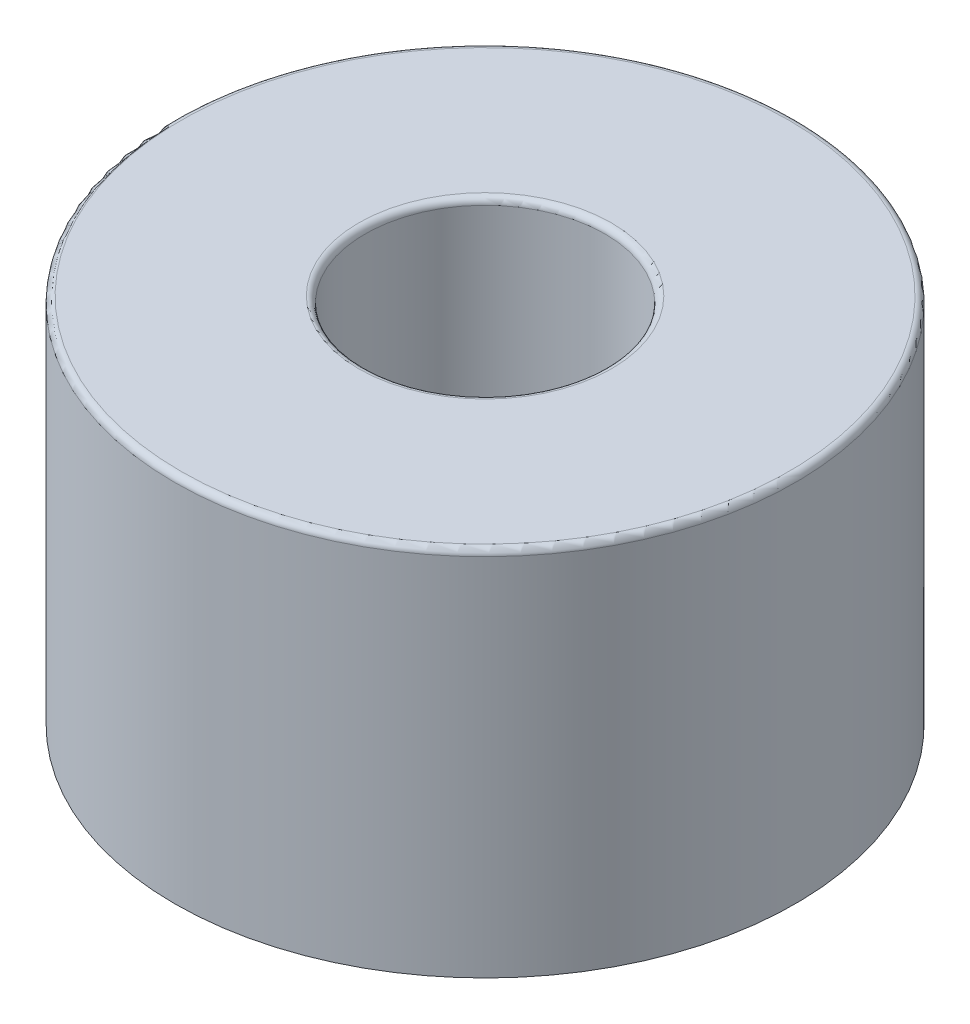
SolidWorks part; units mm, degrees
material "POLYURETHANE (11671)"
ref_plane "Front" through (0, 0, 0) normal (0, 0, 1) x (1, 0, 0)
ref_plane "Top" through (0, 0, 0) normal (0, 1, 0) x (1, 0, 0)
ref_plane "Right" through (0, 0, 0) normal (1, 0, 0) x (0, 0, -1)
sketch "Sketch1" plane through (0, 0, 0) normal (0, 1, 0) x (1, 0, 0)
  circle A0 centre (0, 0) radius 4.7625
  circle A1 centre (0, 0) radius 12.319
  dimension "D1" = 9.525
  dimension "D2" = 24.638
extrude "Boss-Extrude1" add sketch "Sketch1" along normal blind 14.732
fillet "Fillet1" radius 0.254
